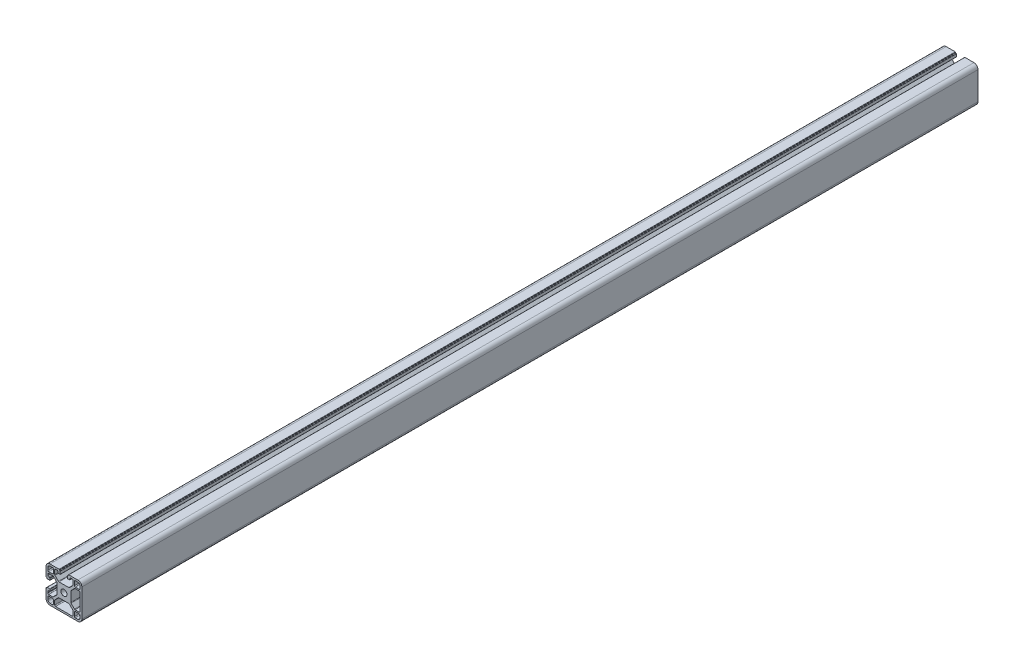
SolidWorks part; units mm, degrees
material "6063 T5"
ref_plane "Спереди" through (0, 0, 0) normal (0, 0, 1) x (1, 0, 0)
ref_plane "Сверху" through (0, 0, 0) normal (0, 1, 0) x (1, 0, 0)
ref_plane "Справа" through (0, 0, 0) normal (1, 0, 0) x (0, 0, -1)
sketch "Эскиз1" plane through (0, 0, 0) normal (0, 0, 1) x (1, 0, 0)
  line L0 (-19.98, 20.5457) -> (20.02, 20.5457) construction
  line L1 (-20, 10.25) -> (-20, 15.5)
  line L2 (-15.5, 20) -> (-10.25, 20)
  line L3 (10.25, 20) -> (15.5, 20)
  line L4 (-12.8, 11.8) -> (-17, 11.8)
  line L5 (-11.8, 12.8) -> (-11.8, 17)
  line L6 (-12.8, 18) -> (-15.5, 18)
  line L7 (-18, 12.8) -> (-18, 15.5)
  line L8 (20, 15.5) -> (20, 10.25)
  line L9 (11.8, 12.8) -> (11.8, 17)
  line L10 (12.8, 11.8) -> (17, 11.8)
  line L11 (18, 12.8) -> (18, 15.5)
  line L12 (12.8, 18) -> (15.5, 18)
  line L13 (20, -10.25) -> (20, -15.5)
  line L14 (15.5, -20) -> (10.25, -20)
  line L15 (12.8, -11.8) -> (17, -11.8)
  line L16 (11.8, -12.8) -> (11.8, -17)
  line L17 (12.8, -18) -> (15.5, -18)
  line L18 (18, -12.8) -> (18, -15.5)
  line L19 (-10.25, -20) -> (-15.5, -20)
  line L20 (-20, -15.5) -> (-20, -10.25)
  line L21 (-11.8, -12.8) -> (-11.8, -17)
  line L22 (-12.8, -11.8) -> (-17, -11.8)
  line L23 (-18, -12.8) -> (-18, -15.5)
  line L24 (-12.8, -18) -> (-15.5, -18)
  line L25 (0, 0) -> (-11.8, 12.8) construction
  line L26 (-20.0122, 26.7385) -> (19.9878, 26.7385) construction
  line L27 (20, -10.25) -> (20, 0)
  line L28 (0, -18) -> (9.25, -18)
  line L29 (10.25, -17) -> (10.25, -12.4642)
  line L30 (9.9571, -11.7571) -> (6.1929, -7.9929)
  line L31 (-5.4858, -7.7) -> (5.4858, -7.7)
  line L32 (-9.9571, -11.7571) -> (-6.1929, -7.9929)
  line L33 (18, 0) -> (18, -9.25)
  line L34 (17, -10.25) -> (12.4642, -10.25)
  line L35 (11.7571, -9.9571) -> (7.9929, -6.1929)
  line L36 (7.7, -5.4858) -> (7.7, 5.4858)
  line L37 (7.7, 0) -> (20, 0) construction
  line L38 (11.7571, 9.9571) -> (7.9929, 6.1929)
  line L39 (17, 10.25) -> (12.4642, 10.25)
  line L40 (18, 0) -> (18, 9.25)
  line L41 (-10.25, -17) -> (-10.25, -12.4642)
  line L42 (0, -18) -> (-9.25, -18)
  line L43 (-10.25, -20) -> (0, -20)
  line L44 (10.25, -20) -> (0, -20)
  line L45 (0, 0) -> (7.7, -5.4858) construction
  line L46 (20, 10.25) -> (20, 0)
  line L47 (0, 0) -> (-5.4858, -7.7) construction
  arc A0 (-20, 15.5) -> (-15.5, 20) centre (-15.5, 15.5) cw
  arc A1 (-15.5, 18) -> (-18, 15.5) centre (-15.5, 15.5) ccw
  arc A2 (-17, 11.8) -> (-18, 12.8) centre (-17, 12.8) cw
  arc A3 (-12.8, 11.8) -> (-11.8, 12.8) centre (-12.8, 12.8) ccw
  arc A4 (-11.8, 17) -> (-12.8, 18) centre (-12.8, 17) ccw
  circle A5 centre (0, 0) radius 3.4
  arc A6 (15.5, 20) -> (20, 15.5) centre (15.5, 15.5) cw
  arc A7 (18, 15.5) -> (15.5, 18) centre (15.5, 15.5) ccw
  arc A8 (11.8, 17) -> (12.8, 18) centre (12.8, 17) cw
  arc A9 (11.8, 12.8) -> (12.8, 11.8) centre (12.8, 12.8) ccw
  arc A10 (17, 11.8) -> (18, 12.8) centre (17, 12.8) ccw
  arc A11 (20, -15.5) -> (15.5, -20) centre (15.5, -15.5) cw
  arc A12 (15.5, -18) -> (18, -15.5) centre (15.5, -15.5) ccw
  arc A13 (17, -11.8) -> (18, -12.8) centre (17, -12.8) cw
  arc A14 (12.8, -11.8) -> (11.8, -12.8) centre (12.8, -12.8) ccw
  arc A15 (11.8, -17) -> (12.8, -18) centre (12.8, -17) ccw
  arc A16 (-15.5, -20) -> (-20, -15.5) centre (-15.5, -15.5) cw
  arc A17 (-18, -15.5) -> (-15.5, -18) centre (-15.5, -15.5) ccw
  arc A18 (-11.8, -17) -> (-12.8, -18) centre (-12.8, -17) cw
  arc A19 (-11.8, -12.8) -> (-12.8, -11.8) centre (-12.8, -12.8) ccw
  arc A20 (-17, -11.8) -> (-18, -12.8) centre (-17, -12.8) ccw
  arc A21 (9.25, -18) -> (10.25, -17) centre (9.25, -17) ccw
  arc A22 (10.25, -12.4642) -> (9.9571, -11.7571) centre (9.25, -12.4642) ccw
  arc A23 (6.1929, -7.9929) -> (5.4858, -7.7) centre (5.4858, -8.7) ccw
  arc A24 (-6.1929, -7.9929) -> (-5.4858, -7.7) centre (-5.4858, -8.7) cw
  arc A25 (-10.25, -12.4642) -> (-9.9571, -11.7571) centre (-9.25, -12.4642) cw
  arc A26 (7.9929, -6.1929) -> (7.7, -5.4858) centre (8.7, -5.4858) cw
  arc A27 (12.4642, -10.25) -> (11.7571, -9.9571) centre (12.4642, -9.25) cw
  arc A28 (18, -9.25) -> (17, -10.25) centre (17, -9.25) cw
  arc A29 (-9.25, -18) -> (-10.25, -17) centre (-9.25, -17) cw
  arc A31 (18, 9.25) -> (17, 10.25) centre (17, 9.25) ccw
  arc A32 (12.4642, 10.25) -> (11.7571, 9.9571) centre (12.4642, 9.25) ccw
  arc A33 (7.9929, 6.1929) -> (7.7, 5.4858) centre (8.7, 5.4858) ccw
  point P5 (0, 0)
  point P77 (7.7, 5.9)
  point P79 (7.7, -5.9)
  line B0 (-20, 10.25) -> (-20, 5.4)
  line B1 (-19.7, 5.1) -> (-19.3, 5.1)
  line B2 (-19, 4.8) -> (-19, 4.4)
  line B3 (-18.7, 4.1) -> (-15.8, 4.1)
  line B4 (-15.5, 4.4) -> (-15.5, 6.3)
  line B5 (-15.8, 6.6) -> (-17, 6.6)
  line B6 (-18, 7.6) -> (-18, 9.25)
  line B7 (-17, 10.25) -> (-12.4642, 10.25)
  line B8 (-11.7571, 9.9571) -> (-7.9929, 6.1929)
  line B9 (-7.7, 5.4858) -> (-7.7, -5.4858)
  line B10 (-7.7, 0) -> (-20, 0) construction
  line B11 (-11.7571, -9.9571) -> (-7.9929, -6.1929)
  line B12 (-17, -10.25) -> (-12.4642, -10.25)
  line B13 (-18, -7.6) -> (-18, -9.25)
  line B14 (-15.8, -6.6) -> (-17, -6.6)
  line B15 (-15.5, -4.4) -> (-15.5, -6.3)
  line B16 (-18.7, -4.1) -> (-15.8, -4.1)
  line B17 (-19, -4.8) -> (-19, -4.4)
  line B18 (-19.7, -5.1) -> (-19.3, -5.1)
  line B19 (-20, -10.25) -> (-20, -5.4)
  arc B20 (-15.5, 6.3) -> (-15.8, 6.6) centre (-15.8, 6.3) ccw
  arc B21 (-15.8, 4.1) -> (-15.5, 4.4) centre (-15.8, 4.4) ccw
  arc B22 (-19, 4.4) -> (-18.7, 4.1) centre (-18.7, 4.4) ccw
  arc B23 (-19.3, 5.1) -> (-19, 4.8) centre (-19.3, 4.8) cw
  arc B24 (-20, 5.4) -> (-19.7, 5.1) centre (-19.7, 5.4) ccw
  arc B25 (-7.9929, 6.1929) -> (-7.7, 5.4858) centre (-8.7, 5.4858) cw
  arc B26 (-12.4642, 10.25) -> (-11.7571, 9.9571) centre (-12.4642, 9.25) cw
  arc B27 (-18, 9.25) -> (-17, 10.25) centre (-17, 9.25) cw
  arc B28 (-17, 6.6) -> (-18, 7.6) centre (-17, 7.6) cw
  arc B29 (-17, -6.6) -> (-18, -7.6) centre (-17, -7.6) ccw
  arc B30 (-18, -9.25) -> (-17, -10.25) centre (-17, -9.25) ccw
  arc B31 (-12.4642, -10.25) -> (-11.7571, -9.9571) centre (-12.4642, -9.25) ccw
  arc B32 (-7.9929, -6.1929) -> (-7.7, -5.4858) centre (-8.7, -5.4858) ccw
  arc B33 (-20, -5.4) -> (-19.7, -5.1) centre (-19.7, -5.4) cw
  arc B34 (-19.3, -5.1) -> (-19, -4.8) centre (-19.3, -4.8) ccw
  arc B35 (-19, -4.4) -> (-18.7, -4.1) centre (-18.7, -4.4) cw
  arc B36 (-15.8, -4.1) -> (-15.5, -4.4) centre (-15.8, -4.4) cw
  arc B37 (-15.5, -6.3) -> (-15.8, -6.6) centre (-15.8, -6.3) cw
  line B38 (10.25, 20) -> (5.4, 20)
  line B39 (5.1, 19.7) -> (5.1, 19.3)
  line B40 (4.8, 19) -> (4.4, 19)
  line B41 (4.1, 18.7) -> (4.1, 15.8)
  line B42 (4.4, 15.5) -> (6.3, 15.5)
  line B43 (6.6, 15.8) -> (6.6, 17)
  line B44 (7.6, 18) -> (9.25, 18)
  line B45 (10.25, 17) -> (10.25, 12.4642)
  line B46 (9.9571, 11.7571) -> (6.1929, 7.9929)
  line B47 (5.4858, 7.7) -> (-5.4858, 7.7)
  line B48 (0, 7.7) -> (0, 20) construction
  line B49 (-9.9571, 11.7571) -> (-6.1929, 7.9929)
  line B50 (-10.25, 17) -> (-10.25, 12.4642)
  line B51 (-7.6, 18) -> (-9.25, 18)
  line B52 (-6.6, 15.8) -> (-6.6, 17)
  line B53 (-4.4, 15.5) -> (-6.3, 15.5)
  line B54 (-4.1, 18.7) -> (-4.1, 15.8)
  line B55 (-4.8, 19) -> (-4.4, 19)
  line B56 (-5.1, 19.7) -> (-5.1, 19.3)
  line B57 (-10.25, 20) -> (-5.4, 20)
  arc B58 (6.3, 15.5) -> (6.6, 15.8) centre (6.3, 15.8) ccw
  arc B59 (4.1, 15.8) -> (4.4, 15.5) centre (4.4, 15.8) ccw
  arc B60 (4.4, 19) -> (4.1, 18.7) centre (4.4, 18.7) ccw
  arc B61 (5.1, 19.3) -> (4.8, 19) centre (4.8, 19.3) cw
  arc B62 (5.4, 20) -> (5.1, 19.7) centre (5.4, 19.7) ccw
  arc B63 (6.1929, 7.9929) -> (5.4858, 7.7) centre (5.4858, 8.7) cw
  arc B64 (10.25, 12.4642) -> (9.9571, 11.7571) centre (9.25, 12.4642) cw
  arc B65 (9.25, 18) -> (10.25, 17) centre (9.25, 17) cw
  arc B66 (6.6, 17) -> (7.6, 18) centre (7.6, 17) cw
  arc B67 (-6.6, 17) -> (-7.6, 18) centre (-7.6, 17) ccw
  arc B68 (-9.25, 18) -> (-10.25, 17) centre (-9.25, 17) ccw
  arc B69 (-10.25, 12.4642) -> (-9.9571, 11.7571) centre (-9.25, 12.4642) ccw
  arc B70 (-6.1929, 7.9929) -> (-5.4858, 7.7) centre (-5.4858, 8.7) ccw
  arc B71 (-5.4, 20) -> (-5.1, 19.7) centre (-5.4, 19.7) cw
  arc B72 (-5.1, 19.3) -> (-4.8, 19) centre (-4.8, 19.3) ccw
  arc B73 (-4.4, 19) -> (-4.1, 18.7) centre (-4.4, 18.7) cw
  arc B74 (-4.1, 15.8) -> (-4.4, 15.5) centre (-4.4, 15.8) cw
  arc B75 (-6.3, 15.5) -> (-6.6, 15.8) centre (-6.3, 15.8) cw
  dimension "D12" = 90
  dimension "D13" = 135
  dimension "D2" = 4.5
  dimension "D3" = 2.5
  dimension "D5" = 1
  dimension "D6" = 6.8
  dimension "D15" = 1
  dimension "D1" = 20
  dimension "D4" = 6.2
  dimension "D7" = 40
  dimension "D8" = 12.3
  dimension "D9" = 11.8
  dimension "D10" = 2
  dimension "D11" = 20.5
  dimension "D18" = 2
sketch_block_instance "8B(20,5PL)-1"
sketch_block "8B(20,5PL)" parameters "D7"=0.3, "D8"=1, "D1"=12.3, "D2"=4.5, "D3"=8.2, "D4"=20.5, "D5"=10.2, "D6"=135, "D9"=4.85, "D10"=2.7, "D11"=1.65
sketch_block_instance "8B(20,5PL)-3"
sketch_block_instance "8B(20,5PL)-6"
sketch_block_instance "8B(20,5PL)-7"
extrude "Бобышка-Вытянуть1" add sketch "Эскиз1" along normal blind 1000
